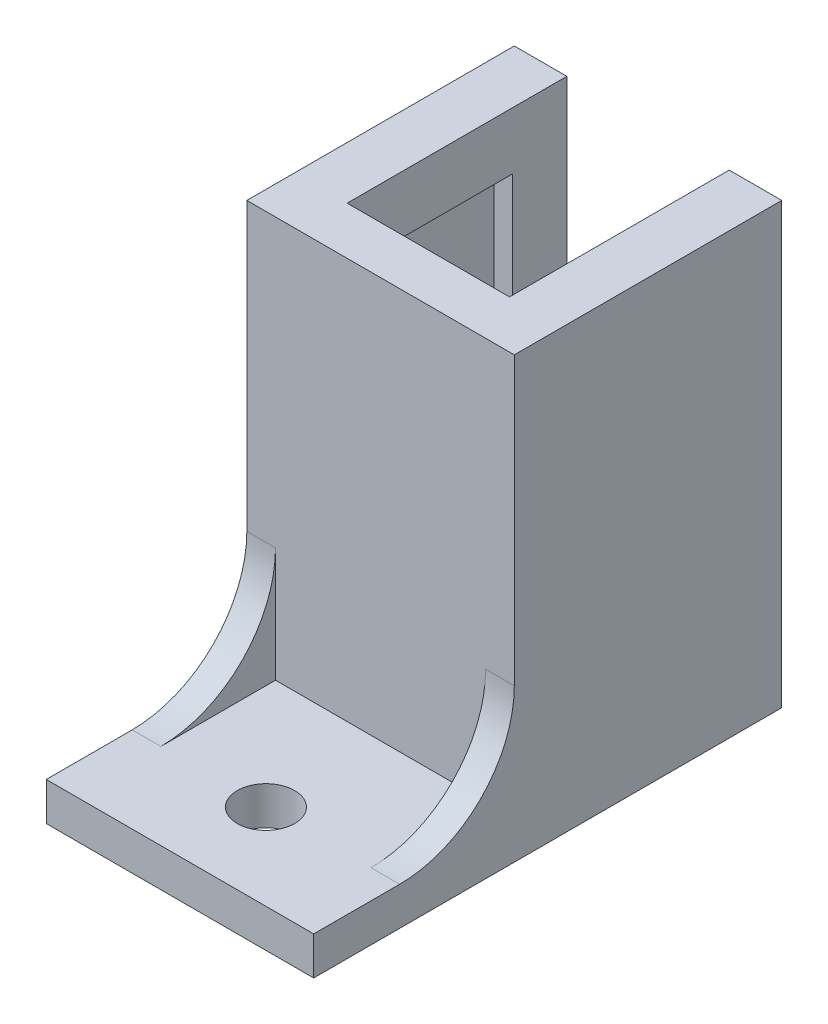
SolidWorks part; units mm, degrees
ref_plane "Front Plane" through (0, 0, 0) normal (0, 0, 1) x (1, 0, 0)
ref_plane "Top Plane" through (0, 0, 0) normal (0, 1, 0) x (1, 0, 0)
ref_plane "Right Plane" through (0, 0, 0) normal (1, 0, 0) x (0, 0, -1)
sketch "Sketch1" plane through (0, 0, 0) normal (0, 0, 1) x (1, 0, 0)
  line L1 (7, 11.5) -> (-7, 11.5)
  line L2 (7, 11.5) -> (7, -11.5)
  line L3 (7, -11.5) -> (-7, -11.5)
  line L4 (-7, 11.5) -> (-7, -11.5)
  line L5 (7, 11.5) -> (-7, -11.5) construction
  line L6 (7, -11.5) -> (-7, 11.5) construction
  point P0 (0, 0)
  dimension "D1" = 14
  dimension "D2" = 23
extrude "Boss-Extrude1" add sketch "Sketch1" along normal blind 14
sketch "Sketch2" plane through (0, -11.5, 0) normal (0, -1, 0) x (1, 0, 0)
  line L1 (5.2, 2.85) -> (-5.2, 2.85)
  line L2 (5.2, 2.85) -> (5.2, 11.5)
  line L3 (5.2, 11.5) -> (-5.2, 11.5)
  line L4 (-5.2, 2.85) -> (-5.2, 11.5)
  line L8 (4.25, 2.85) -> (-4.25, 2.85)
  line L9 (4.25, 2.85) -> (4.25, 0)
  line L10 (4.25, 0) -> (-4.25, 0)
  line L11 (-4.25, 2.85) -> (-4.25, 0)
  point P4 (0, 2.85)
  point P16 (0, 0)
  dimension "D1" = 11.5
  dimension "D2" = 8.65
  dimension "D3" = 10.4
  dimension "D4" = 8.5
extrude "Cut-Extrude1" cut sketch "Sketch2" against normal blind 20
sketch "Sketch3" plane through (0, -11.5, 0) normal (0, -1, 0) x (1, 0, 0)
  line L0 (0, 20) -> (0, 14) construction
  line L1 (7, 14) -> (-7, 14)
  line L2 (7, 14) -> (7, 24.5)
  line L3 (7, 24.5) -> (-7, 24.5)
  line L4 (-7, 14) -> (-7, 24.5)
  circle A1 centre (0, 20) radius 1.5
  point P7 (0, 19.4596)
  dimension "D1" = 3
  dimension "D2" = 6
  dimension "D3" = 4.5
extrude "Boss-Extrude2" add sketch "Sketch3" against normal blind 2
sketch "Sketch4" plane through (-7, 0, 0) normal (-1, 0, 0) x (0, 0, 1)
  line L1 (24.5, -9.5) -> (14, -9.5) construction
  line L2 (14, 11.5) -> (14, -9.5) construction
  line L3 (14, -3.5) -> (14, -9.5)
  line L4 (14, -9.5) -> (20, -9.5)
  arc A0 (20, -9.5) -> (14, -3.5) centre (20, -3.5) cw
  dimension "D1" = 6
extrude "Boss-Extrude3" add sketch "Sketch4" against normal blind 1.5
mirror "Mirror1" about plane through (0, 0, 0) normal (1, 0, 0) of "Boss-Extrude3"
sketch "Sketch5" plane through (0, 8.5, 0) normal (0, -1, 0) x (1, 0, 0)
  line L0 (5.2, 11.5) -> (-5.2, 11.5) construction
  line L1 (4.25, 0) -> (-4.25, 0)
  line L2 (4.25, 0) -> (4.25, 11.5)
  line L3 (4.25, 11.5) -> (-4.25, 11.5)
  line L4 (-4.25, 0) -> (-4.25, 11.5)
  line L5 (7, 0) -> (4.25, 0) construction
  line L6 (-4.25, 0) -> (4.25, 0) construction
extrude "Cut-Extrude2" cut sketch "Sketch5" against normal through all
sketch "Sketch6" plane through (0, 0, 0) normal (0, 0, -1) x (-1, 0, 0)
  line L0 (-7, 11.5) -> (-7, -11.5) construction
  line L1 (-7, 0) -> (7, 0)
  line L2 (-7, 0) -> (-7, -11.5)
  line L3 (-7, -11.5) -> (7, -11.5)
  line L4 (7, 0) -> (7, -11.5)
extrude "Cut-Extrude3" [suppressed] cut sketch "Sketch6" against normal through all
